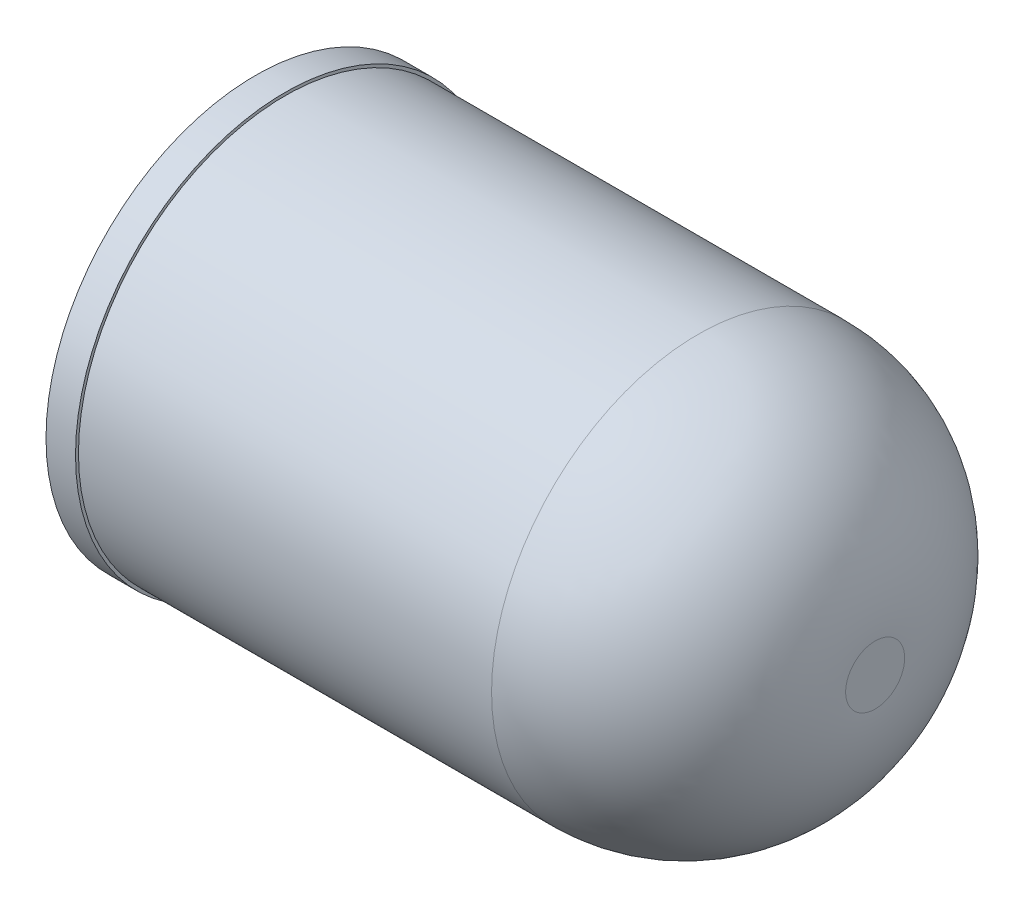
SolidWorks part; units mm, degrees
material "Aleación 1060"
ref_plane "Alzado" through (0, 0, 0) normal (0, 0, 1) x (1, 0, 0)
ref_plane "Planta" through (0, 0, 0) normal (0, 1, 0) x (1, 0, 0)
ref_plane "Vista lateral" through (0, 0, 0) normal (1, 0, 0) x (0, 0, -1)
sketch "Croquis1" plane through (0, 0, 0) normal (1, 0, 0) x (0, 0, -1)
  circle A0 centre (0, 0) radius 3.5
  dimension "D1" = 7
extrude "Saliente-Extruir1" add sketch "Croquis1" along normal blind 10
fillet "Redondeo1" radius 3 1 edges at (10, 0, -3.5)
sketch "Croquis2" plane through (0, 0, 0) normal (-1, 0, 0) x (0, 0, 1)
  circle A0 centre (0, 0) radius 3.55
  dimension "D1" = 7.1
extrude "Saliente-Extruir2" add sketch "Croquis2" along normal blind 0.5
